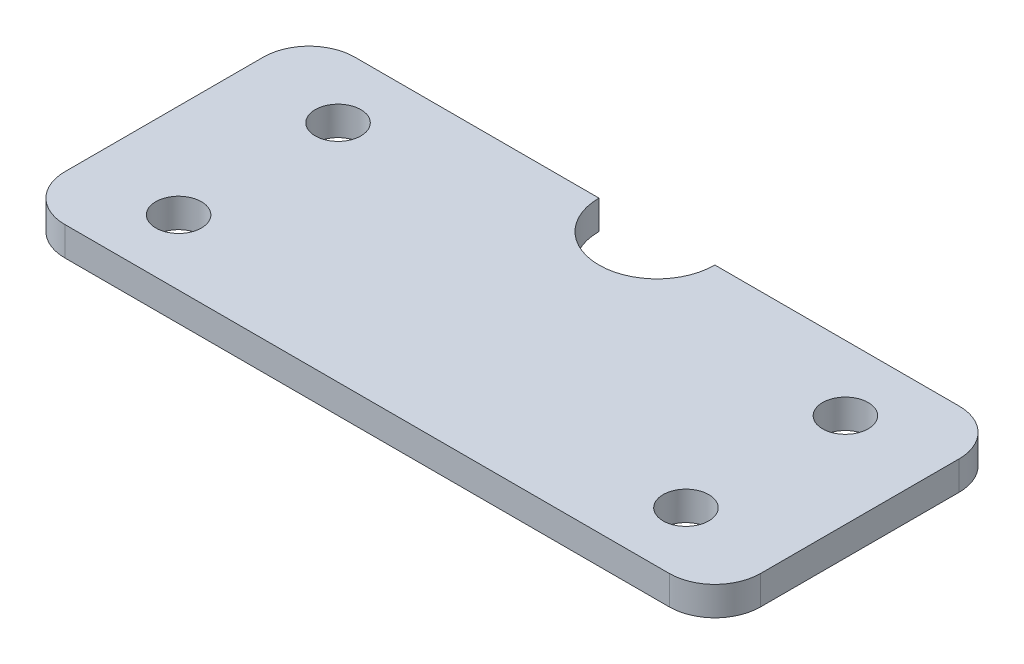
SolidWorks part; units mm, degrees
ref_plane "Front Plane" through (0, 0, 0) normal (0, 0, 1) x (1, 0, 0)
ref_plane "Top Plane" through (0, 0, 0) normal (0, 1, 0) x (1, 0, 0)
ref_plane "Right Plane" through (0, 0, 0) normal (1, 0, 0) x (0, 0, -1)
sketch "Sketch1" plane through (0, 0, 0) normal (0, 1, 0) x (1, 0, 0)
  line L1 (-76.2, -31.75) -> (76.2, -31.75)
  line L2 (-76.2, -31.75) -> (-76.2, 31.75)
  line L3 (-76.2, 31.75) -> (76.2, 31.75)
  line L4 (76.2, -31.75) -> (76.2, 31.75)
  line L5 (-76.2, -31.75) -> (76.2, 31.75) construction
  line L6 (-76.2, 31.75) -> (76.2, -31.75) construction
  point P0 (0, 0)
  dimension "D1" = 63.5
  dimension "D2" = 152.4
extrude "Boss-Extrude1" add sketch "Sketch1" along normal blind 6.35
sketch "Sketch2" plane through (0, 6.35, 0) normal (0, 1, 0) x (1, 0, 0)
  line L0 (0, 4.571) -> (0, 14.646) construction
  line L1 (0, 0) -> (10.2652, 0) construction
  circle A0 centre (-55.5625, 17.4625) radius 5
  circle A6 centre (55.5625, 17.4625) radius 5
  circle A7 centre (55.5625, -17.4625) radius 5
  circle A10 centre (-55.5625, -17.4625) radius 5
  dimension "D1" = 10
  dimension "D2" = 55.5625
  dimension "D3" = 17.4625
fillet "Fillet1" radius 10 4 edges at (-76.2, 3.175, 31.75) (76.2, 3.175, 31.75) (76.2, 3.175, -31.75) (-76.2, 3.175, -31.75)
sketch "Sketch3" plane through (0, 6.35, 0) normal (0, 1, 0) x (1, 0, 0)
  line L4 (0, 0) -> (-64.7181, 0) construction
  line L5 (-12.7, 31.75) -> (12.7, 31.75)
  arc A1 (12.7, 31.75) -> (-12.7, 31.75) centre (0, 31.75) cw
extrude "Cut-Extrude4" cut sketch "Sketch3" against normal blind 6.35
extrude "Cut-Extrude5" cut sketch "Sketch2" against normal blind 10
